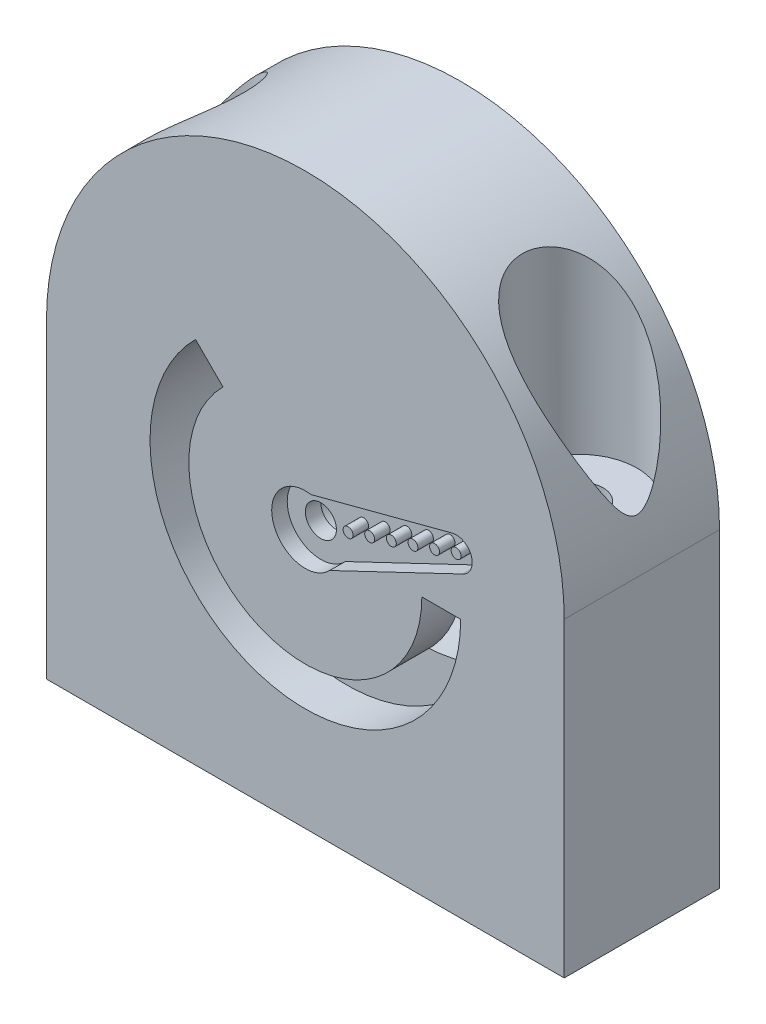
SolidWorks part; units mm, degrees
material "ABS"
ref_plane "Ön Düzlem" through (0, 0, 0) normal (0, 0, 1) x (1, 0, 0)
ref_plane "Üst Düzlem" through (0, 0, 0) normal (0, 1, 0) x (1, 0, 0)
ref_plane "Sağ Düzlem" through (0, 0, 0) normal (1, 0, 0) x (0, 0, -1)
other "abs"
sketch "Sketch1" plane through (0, 0, 0) normal (0, 0, 1) x (1, 0, 0)
  line L1 (25, 0) -> (25, -30)
  line L2 (25, -30) -> (-25, -30)
  line L3 (-25, -30) -> (-25, 0)
  arc A0 (25, 0) -> (-25, 0) centre (0, 0) ccw
  dimension "D1" = 30
  dimension "D2" = 25
  dimension "D4" = 50
extrude "Boss-Extrude1" add sketch "Sketch1" along normal blind 15
sketch "Sketch2" plane through (0, -30, 0) normal (0, -1, 0) x (1, 0, 0)
  line L2 (0, 0) -> (0, 19.4888) construction
  line L3 (-25, 0) -> (25, 0) construction
  circle A0 centre (-19, 7.5) radius 2.25
  circle A1 centre (19, 7.5) radius 2.25
  dimension "D1" = 4.5
  dimension "D2" = 19
  dimension "D3" = 7.5
extrude "Cut-Extrude1" cut sketch "Sketch2" against normal up to next
ref_plane "Plane1" through (0, 24.1271, 0) normal (0, 1, 0) x (1, 0, 0)
sketch "Sketch3" plane through (0, 24.1271, 0) normal (0, 1, 0) x (1, 0, 0)
  line L1 (0, 0) -> (0, -27.0205) construction
  circle A0 centre (19, -7.5) radius 5.54
  circle A1 centre (-19, -7.5) radius 5.54
  dimension "D1" = 11.08
  dimension "D2" = 19
extrude "Cut-Extrude2" cut sketch "Sketch3" against normal blind 21
sketch "Sketch4" plane through (0, -30, 0) normal (0, -1, 0) x (1, 0, 0)
  line L0 (-25, 0) -> (25, 0) construction
  line L1 (12, 4) -> (-12, 4)
  line L2 (12, 4) -> (12, 11)
  line L3 (12, 11) -> (-12, 11)
  line L4 (-12, 4) -> (-12, 11)
  line L5 (12, 4) -> (-12, 11) construction
  line L6 (12, 11) -> (-12, 4) construction
  line L7 (25, 15) -> (25, 0) construction
  point P0 (0, 7.5)
  dimension "D1" = 7.5
  dimension "D2" = 25
  dimension "D3" = 7
  dimension "D4" = 24
extrude "Cut-Extrude3" cut sketch "Sketch4" against normal blind 29
sketch "Sketch5" plane through (0, 0, 15) normal (0, 0, 1) x (1, 0, 0)
  line L0 (-19.9055, -5) -> (17.8455, -5) construction
  line L2 (11.2517, -5) -> (15, -5)
  line L3 (0, 10.1581) -> (0, -23.5491) construction
  line L4 (-7.9562, 2.9562) -> (-10.6066, 5.6066)
  arc A0 (-15, -5) -> (15, -5) centre (0, -5) ccw
  arc A1 (-11.2517, -5) -> (11.2517, -5) centre (0, -5) ccw
  arc A2 (-11.2517, -5) -> (-7.9562, 2.9562) centre (0, -5) cw
  arc A3 (-15, -5) -> (-10.6066, 5.6066) centre (0, -5) cw
  dimension "D2" = 15
  dimension "D1" = 11.2517
  dimension "D3" = 11.2517
extrude "Cut-Extrude4" cut sketch "Sketch5" against normal up to next
sketch "Sketch6" plane through (0, 0, 15) normal (0, 0, 1) x (1, 0, 0)
  line L0 (0, -5) -> (20.5433, 2.4771) construction
  line L1 (0, -5) -> (22.295, -5) construction
  line L2 (0.5415, -1.7954) -> (14.1698, 1.8)
  line L4 (2.3529, -7.2419) -> (15.1898, -1.1173)
  arc A0 (0.5415, -1.7954) -> (2.3529, -7.2419) centre (0, -5) ccw
  arc A2 (15.1898, -1.1173) -> (14.1698, 1.8) centre (14.5652, 0.3013) ccw
  dimension "D1" = 15.5
  dimension "D3" = 3.1
  dimension "D4" = 6.5
  dimension "D2" = 20
extrude "Cut-Extrude5" cut sketch "Sketch6" against normal blind 1.5 contours A0 L4 A2 L2
sketch "Sketch7" plane through (0, 0, 13.5) normal (0, 0, 1) x (1, 0, 0)
  circle A0 centre (0, -5) radius 3.25
extrude "Boss-Extrude2" add sketch "Sketch7" against normal up to surface (13.5 mm away) up to face at (-1.5504, -8.743, 0)
sketch "Sketch8" plane through (0, 0, 13.5) normal (0, 0, 1) x (1, 0, 0)
  circle A0 centre (0, -5) radius 1.5
  dimension "D1" = 3
extrude "Cut-Extrude6" cut sketch "Sketch8" against normal up to next
sketch "Sketch9" plane through (0, 0, 0) normal (0, 0, -1) x (-1, 0, 0)
  circle A0 centre (0, -5) radius 2.5
  dimension "D1" = 5
extrude "Cut-Extrude7" cut sketch "Sketch9" against normal offset from surface (12 mm away) 1.5 up to face at (1.5, -5, 13.5)
sketch "Sketch10" plane through (0, 0, 13.5) normal (0, 0, 1) x (1, 0, 0)
  line L0 (14.5652, 0.3013) -> (4.27, -3.5799) construction
  circle A0 centre (14.5652, 0.3013) radius 0.48
  circle A1 centre (12.4777, -0.393) radius 0.48
  circle A2 centre (10.3901, -1.0872) radius 0.48
  circle A3 centre (8.3025, -1.7815) radius 0.48
  circle A4 centre (6.2149, -2.4758) radius 0.48
  circle A5 centre (4.1273, -3.17) radius 0.48
  dimension "D1" = 6
extrude "Boss-Extrude3" add sketch "Sketch10" along normal blind 1.5
